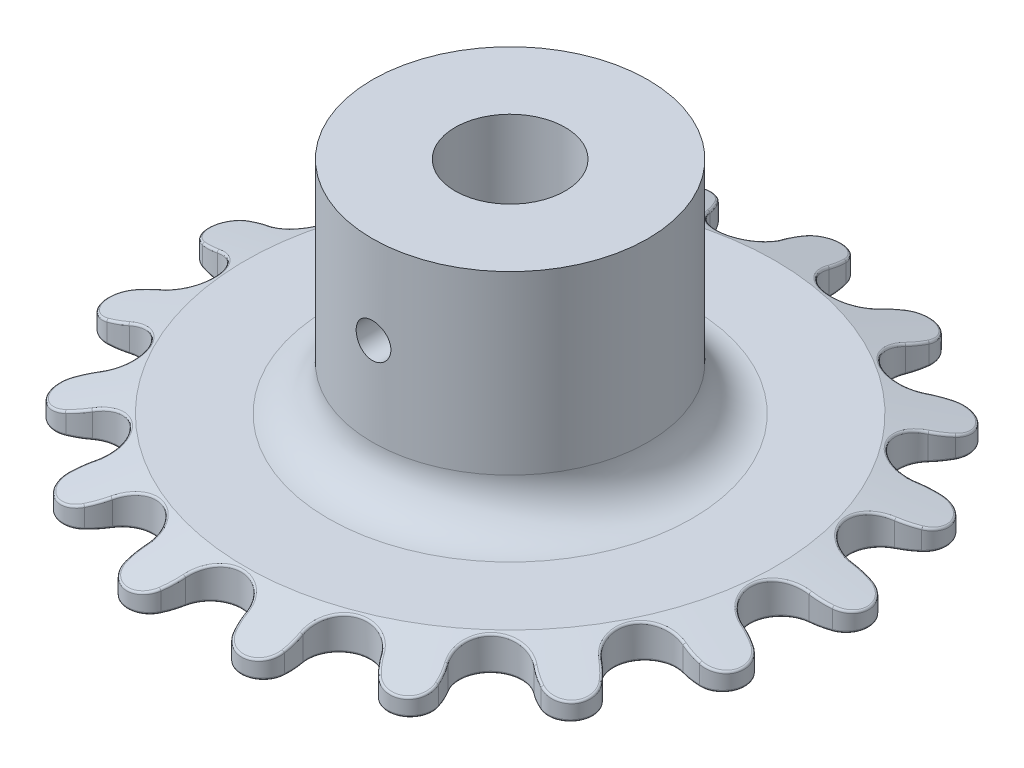
SolidWorks part; units mm, degrees
ref_plane "Front Plane" through (0, 0, 0) normal (0, 0, 1) x (1, 0, 0)
ref_plane "Top Plane" through (0, 0, 0) normal (0, 1, 0) x (1, 0, 0)
ref_plane "Right Plane" through (0, 0, 0) normal (1, 0, 0) x (0, 0, -1)
sketch "Sketch1" plane through (0, 0, 0) normal (0, 1, 0) x (1, 0, 0)
  line L0 (0, 0) -> (0, 16.9847) construction
  line L1 (0, 16.9847) -> (-3.175, 16.9847) construction
  line L2 (0, 16.9847) -> (3.175, 16.9847) construction
  line L3 (-3.175, 16.9847) -> (0, 0) construction
  line L4 (0, 0) -> (3.175, 16.9847) construction
  line L5 (-2.8716, 15.3619) -> (0, 0)
  line L6 (0, 0) -> (2.8716, 15.3619)
  line L7 (0, 17.279) -> (0, 17.787) construction
  arc A0 (-2.8716, 15.3619) -> (-1.524, 16.9847) centre (-3.175, 16.9847) ccw
  arc A1 (1.524, 16.9847) -> (2.8716, 15.3619) centre (3.175, 16.9847) ccw
  arc A2 (1.524, 16.9847) -> (1.3808, 18.1358) centre (-3.175, 16.9847) ccw
  arc A3 (-1.524, 16.9847) -> (-1.3808, 18.1358) centre (3.175, 16.9847) cw
  arc A4 (-1.524, 16.9847) -> (-2.8716, 15.3619) centre (-3.175, 16.9847) ccw construction
  arc A5 (2.8716, 15.3619) -> (1.524, 16.9847) centre (3.175, 16.9847) ccw construction
  circle A6 centre (0, 0) radius 17.279 construction
  arc A7 (-1.3808, 18.1358) -> (1.3808, 18.1358) centre (0, 17.787) cw
  arc A8 (-1.3808, 18.1358) -> (0, 20.4488) centre (3.175, 16.9847) cw construction
  arc A9 (1.3808, 18.1358) -> (0, 20.4488) centre (-3.175, 16.9847) ccw construction
  arc A10 (-2.8483, 15.237) -> (-1.397, 16.9847) centre (-3.175, 16.9847) ccw
  arc A11 (-1.397, 16.9847) -> (-1.2577, 18.1047) centre (3.175, 16.9847) cw
  arc A12 (-1.2577, 18.1047) -> (1.2577, 18.1047) centre (0, 17.787) cw
  arc A13 (1.397, 16.9847) -> (1.2577, 18.1047) centre (-3.175, 16.9847) ccw
  arc A14 (1.397, 16.9847) -> (2.8483, 15.237) centre (3.175, 16.9847) ccw
  dimension "D1" = 3.302
  dimension "D2" = 6.35
  dimension "D3" = 21.176
  dimension "D4" = 0.508
  dimension "D5" = 0.127
extrude "Boss-Extrude1" add sketch "Sketch1" along normal mid plane 2.032 contours A14 A13 A12 A11 A10 L5 L6
pattern_circular "CirPattern1" count 17 over 360 about axis through (0, 0, 0) along (0, 1, 0) of "Boss-Extrude1"
sketch "Sketch3" plane through (0, 1.016, 0) normal (0, 1, 0) x (1, 0, 0)
  circle A0 centre (0, 0) radius 3.175
  dimension "D1" = 6.35
extrude "Cut-Extrude1" cut sketch "Sketch3" against normal through all
sketch "Sketch2" plane through (0, 1.016, 0) normal (0, 1, 0) x (1, 0, 0)
  circle A0 centre (0, 0) radius 7.9375
  circle A3 centre (0, 0) radius 3.175 construction
  circle A4 centre (0, 0) radius 3.175
  dimension "D1" = 15.875
extrude "Boss-Extrude2" add sketch "Sketch2" along normal blind 12.7
fillet "Fillet1" radius 2.54 1 edges at (0, 1.016, 7.9375)
sketch "Sketch4" plane through (0, 0, 0) normal (0, 0, 1) x (1, 0, 0)
  line L0 (0, 3.556) -> (0, 13.716) construction
  line L3 (7.9375, 3.556) -> (-7.9375, 3.556) construction
  line L4 (7.9375, 13.716) -> (-7.9375, 13.716) construction
  circle A0 centre (0, 8.636) radius 1
  point P4 (0, 3.81)
  point P6 (0, 13.97)
  point P8 (0, 8.636)
  dimension "D1" = 2
extrude "Cut-Extrude2" cut sketch "Sketch4" against normal through all both and the other way through all
sketch "Sketch5" plane through (0, 0, 0) normal (1, 0, 0) x (0, 0, -1)
  line L0 (19.0842, 1.016) -> (18.1047, 1.016) construction
  line L1 (19.0842, 1.016) -> (18.1047, 1.016)
  line L2 (18.1047, -1.016) -> (19.0842, -1.016) construction
  line L3 (18.1047, -1.016) -> (19.0842, -1.016)
  line L4 (19.0842, 1.016) -> (19.0842, -1.016)
  line L5 (19.0842, 0) -> (15.2742, 1.016)
  line L6 (15.3332, 1.016) -> (12.9129, 1.016) construction
  line L7 (19.0842, 1.016) -> (15.2742, 1.016)
  line L8 (0, 0) -> (0, 14.7034) construction
  dimension "D1" = 1.016
  dimension "D2" = 3.81
revolve "Cut-Revolve1" cut sketch "Sketch5" angle 360 about L8
fillet "Fillet2" radius 0.127 136 edges at (-1.362, -1.016, -17.5491) (0, -1.016, -19.0842) (1.362, -1.016, -17.5491) (2.8483, -1.016, -15.237) (7.6095, -1.016, -15.872) (-3.5559, 0.0002, 18.7491) (-5.5804, 0.9555, 14.4618) (-10.0888, 0.0002, 16.1984) (-10.4277, 0.9555, 11.4694) (-15.2591, 0.0002, 11.46) (-13.8667, 0.9555, 6.928) (-18.3685, 0.0002, 5.1739) (-15.433, 0.9555, 1.4513) (-18.9972, 0.0002, -1.8106) (-14.915, 0.9555, -4.2222) (-17.0601, 0.0002, -8.5512) (-12.3826, 0.9555, -9.325) (-12.819, 0.0002, -14.1366) (-8.1779, 0.9555, -13.1684) (-6.8466, 0.0002, -17.8128) (-2.869, 0.9555, -15.2333) (0.0504, 0.0002, -19.0832) (2.828, 0.9555, -15.2409) (6.9406, 0.0002, -17.7764) (8.1427, 0.9555, -13.1902) (12.8935, 0.0002, -14.0687) (12.3576, 0.9555, -9.358) (17.1051, 0.0002, -8.461) (14.9036, 0.9555, -4.2622) (19.0064, 0.0002, -1.7106) (15.4369, 0.9555, 1.4097) (18.341, 0.0002, 5.2707) (13.8852, 0.9555, 6.8909) (15.1984, 0.0002, 11.5404) (10.4583, 0.9555, 11.4415) (10.0031, 0.0002, 16.2514) (5.6191, 0.9555, 14.4468) (3.4569, 0.0002, 18.7675) (0.0207, 0.9555, 15.5011) (8.1602, -1.016, -13.1792) (10.8162, -1.016, -13.8865) (12.8569, -1.016, -14.1034) (12.37, -1.016, -9.3414) (15.1022, -1.016, -9.0415) (17.0835, -1.016, -8.5066) (14.9092, -1.016, -4.242) (17.3485, -1.016, -2.9755) (19.0028, -1.016, -1.7609) (15.4348, -1.016, 1.4302) (17.2519, -1.016, 3.4925) (18.3557, -1.016, 5.2226) (13.8759, -1.016, 6.9094) (14.8253, -1.016, 9.4887) (15.2295, -1.016, 11.5008) (10.4429, -1.016, 11.4553) (10.3964, -1.016, 14.2035) (10.0465, -1.016, 16.2257) (5.5996, -1.016, 14.4542) (4.5635, -1.016, 17) (3.5067, -1.016, 18.7592) (0, -1.016, 15.501) (-1.8858, -1.016, 17.5005) (-3.5067, -1.016, 18.7592) (-5.5996, -1.016, 14.4542) (-8.0804, -1.016, 15.6375) (-10.0465, -1.016, 16.2257) (-10.4429, -1.016, 11.4553) (-13.1836, -1.016, 11.6626) (-15.2295, -1.016, 11.5008) (-13.8759, -1.016, 6.9094) (-16.5064, -1.016, 6.1126) (-18.3557, -1.016, 5.2226) (-15.4348, -1.016, 1.4302) (-17.5999, -1.016, -0.263) (-19.0028, -1.016, -1.7609) (-14.9092, -1.016, -4.242) (-16.3164, -1.016, -6.603) (-17.0835, -1.016, -8.5066) (-12.37, -1.016, -9.3414) (-12.8293, -1.016, -12.0513) (-12.8569, -1.016, -14.1034) (-8.1602, -1.016, -13.1792) (-7.6095, -1.016, -15.872) (-6.894, -1.016, -17.7955) (5.0694, -1.016, -16.856) (6.894, -1.016, -17.7955) (12.8293, -1.016, -12.0513) (16.3164, -1.016, -6.603) (17.5999, -1.016, -0.263) (16.5064, -1.016, 6.1126) (13.1836, -1.016, 11.6626) (8.0804, -1.016, 15.6375) (1.8858, -1.016, 17.5005) (-4.5635, -1.016, 17) (-10.3964, -1.016, 14.2035) (-14.8253, -1.016, 9.4887) (-17.2519, -1.016, 3.4925) (-17.3485, -1.016, -2.9755) (-15.1022, -1.016, -9.0415) (-10.8162, -1.016, -13.8865) (-5.0694, -1.016, -16.856) (-2.8483, -1.016, -15.237)
equation "\"pitch\"= .25in"
equation "\"roller_OD\"= .13in"
equation "\"num_teeth\"= 17"
equation "\"D1@Sketch1\"=\"roller_OD\""
equation "\"D2@Sketch1\"=\"pitch\""
equation "\"D3@Sketch1\"=360/\"num_teeth\""
equation "\"D1@CirPattern1\"=\"num_teeth\""
